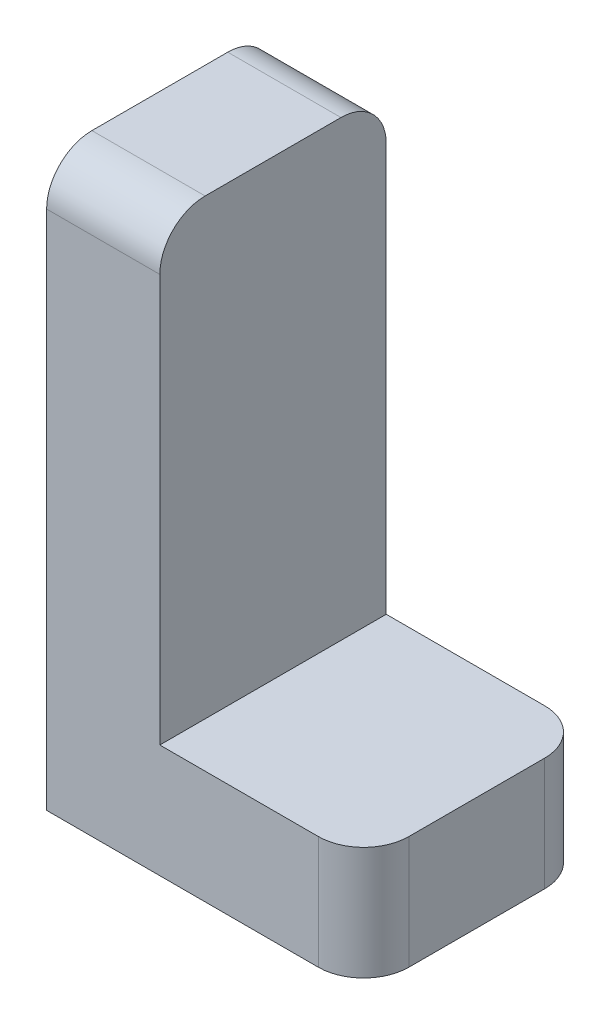
SolidWorks part; units mm, degrees
ref_plane "Front Plane" through (0, 0, 0) normal (0, 0, 1) x (1, 0, 0)
ref_plane "Top Plane" through (0, 0, 0) normal (0, 1, 0) x (1, 0, 0)
ref_plane "Right Plane" through (0, 0, 0) normal (1, 0, 0) x (0, 0, -1)
sketch "Sketch1" plane through (0, 0, 0) normal (0, 0, 1) x (1, 0, 0)
  line L0 (14, 0) -> (0, 0)
  line L1 (0, 0) -> (0, 25)
  line L2 (14, 5) -> (5, 5)
  line L3 (5, 5) -> (5, 25)
  line L4 (0, 25) -> (5, 25)
  line L5 (14, 5) -> (14, 0)
  dimension "D1" = 14
  dimension "D2" = 25
  dimension "D3" = 5
extrude "Boss-Extrude1" add sketch "Sketch1" along normal blind 10
fillet "Fillet1" radius 2 1 edges at (2.5, 25, 10)
fillet "Fillet2" radius 2 1 edges at (2.5, 25, 0)
fillet "Fillet3" radius 2 1 edges at (14, 2.5, 10)
fillet "Fillet4" radius 2 1 edges at (14, 2.5, 0)
sketch "Sketch2" plane through (0, 0, 0) normal (0, -1, 0) x (1, 0, 0)
  line L5 (1.0844, 8.7919) -> (12.2654, 8.7919)
  line L6 (1.0844, 8.7919) -> (1.0844, 1.5619)
  line L7 (1.0844, 1.5619) -> (12.2654, 1.5619)
  line L8 (12.2654, 8.7919) -> (12.2654, 1.5619)
extrude "Cut-Extrude1" cut sketch "Sketch2" against normal blind 4
